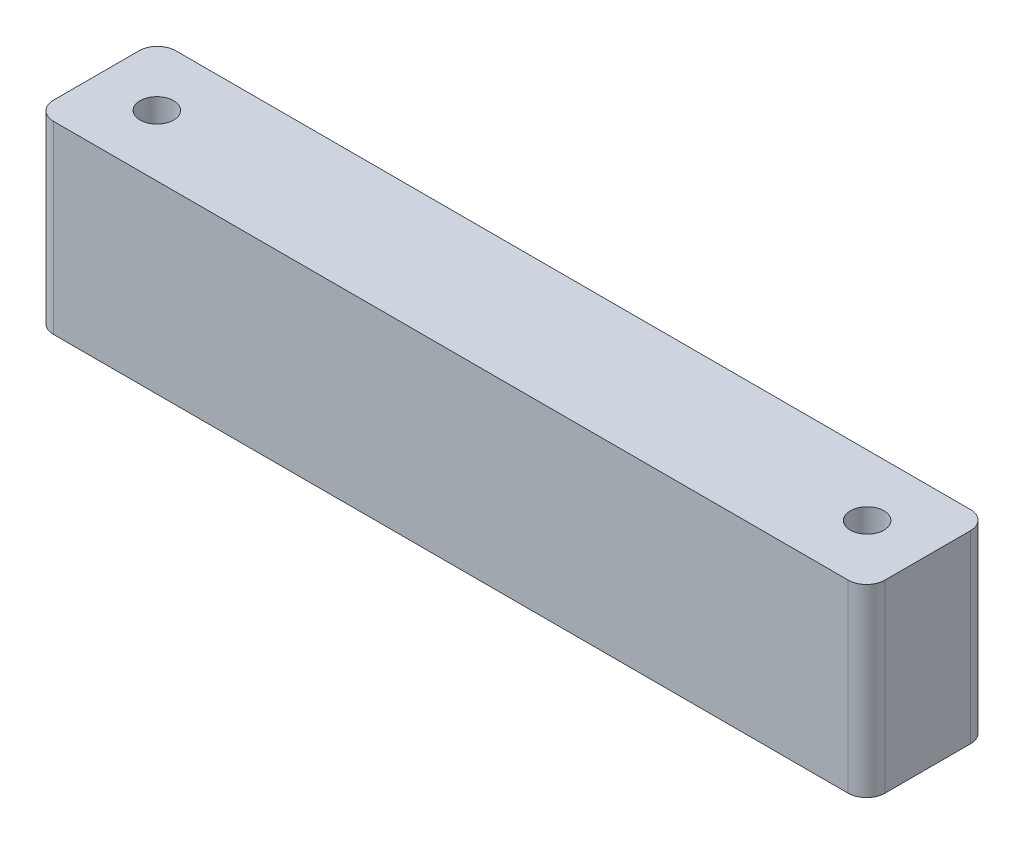
SolidWorks part; units mm, degrees
material "ABS"
ref_plane "Front Plane" through (0, 0, 0) normal (0, 0, 1) x (1, 0, 0)
ref_plane "Top Plane" through (0, 0, 0) normal (0, 1, 0) x (1, 0, 0)
ref_plane "Right Plane" through (0, 0, 0) normal (1, 0, 0) x (0, 0, -1)
sketch "Sketch1" plane through (0, 0, 0) normal (0, 1, 0) x (1, 0, 0)
  line L1 (65, -10) -> (-65, -10)
  line L2 (68, -7) -> (68, 7)
  line L3 (65, 10) -> (-65, 10)
  line L4 (-68, -7) -> (-68, 7)
  line L5 (68, -10) -> (-68, 10) construction
  line L6 (68, 10) -> (-68, -10) construction
  arc A0 (65, -10) -> (68, -7) centre (65, -7) ccw
  arc A1 (68, 7) -> (65, 10) centre (65, 7) ccw
  arc A2 (-65, 10) -> (-68, 7) centre (-65, 7) ccw
  arc A3 (-65, -10) -> (-68, -7) centre (-65, -7) cw
  point P0 (0, 0)
  dimension "D3" = 3
  dimension "D1" = 136
  dimension "D2" = 20
extrude "Boss-Extrude1" add sketch "Sketch1" along normal blind 30.2
sketch "Sketch2" plane through (0, 30.2, 0) normal (0, 1, 0) x (1, 0, 0)
  line L0 (0, -20.1339) -> (0, 23.9222) construction
  point P0 (-58.1, 0)
  point P1 (58.1, 0)
  point P5 (0, 0)
  dimension "D1" = 116.2
hole_wizard "M5 Clearance Hole1" positions "Sketch3" profile "Sketch4" hole size "M5" standard "ANSI Metric" end condition up to next
sketch "Sketch3" plane through (0, 30.2, 0) normal (0, 1, 0) x (1, 0, 0)
  point P0 (-58.1, 0)
  point P3 (58.1, 0)
sketch "Sketch4" plane through (-58.1, 30.2, 0) normal (1, 0, 0) x (0, 0, 1)
  line L0 (0, 0) -> (0, 30.2)
  line L1 (0, 30.2) -> (2.75, 30.2)
  line L2 (2.75, 30.2) -> (2.75, 0)
  line L5 (2.75, 0) -> (0, 0)
  line L11 (0, -6.35) -> (0, 107.95) construction
  dimension "Thru Hole Dia." = 5.5
  dimension "Thru Hole Depth" = 30.2
